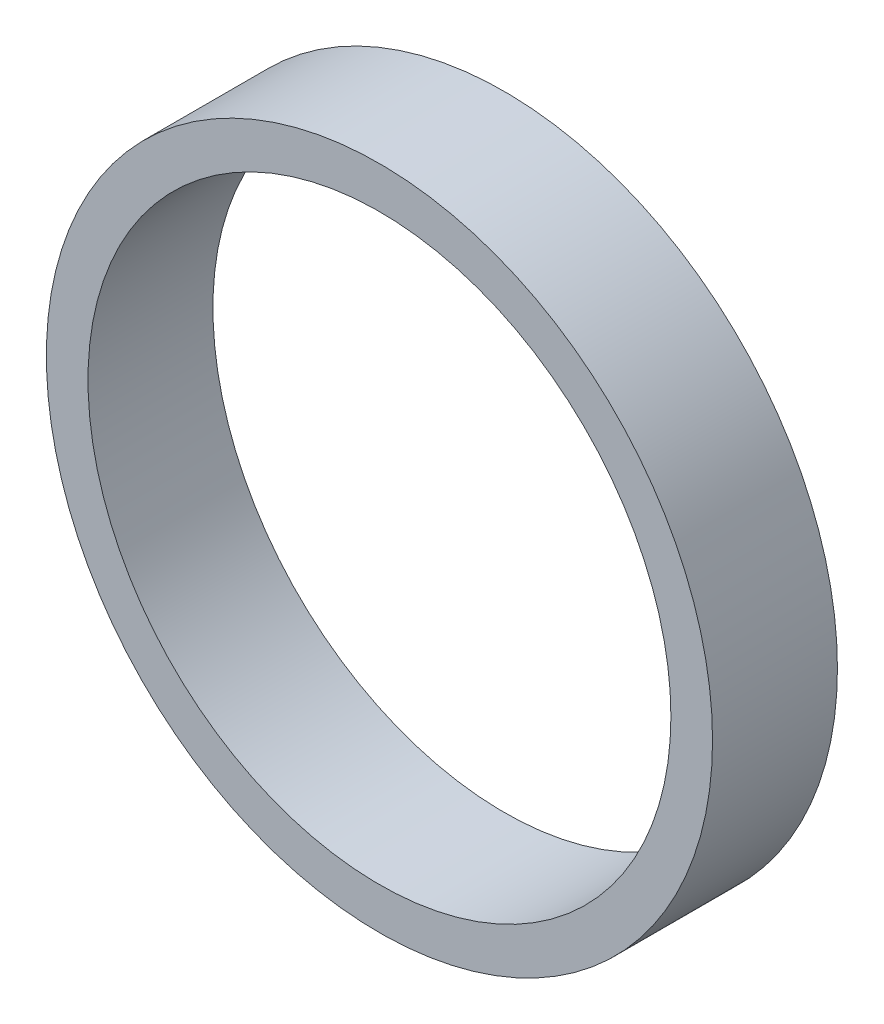
SolidWorks part; units mm, degrees
material "硅橡胶"
ref_plane "前视基准面" through (0, 0, 0) normal (0, 0, 1) x (1, 0, 0)
ref_plane "上视基准面" through (0, 0, 0) normal (0, 1, 0) x (1, 0, 0)
ref_plane "右视基准面" through (0, 0, 0) normal (1, 0, 0) x (0, 0, -1)
sketch "草图1" plane through (0, 0, 0) normal (0, 0, 1) x (1, 0, 0)
  circle A0 centre (0, 0) radius 14
  circle A1 centre (0, 0) radius 16
  dimension "D1" = 28
  dimension "D2" = 32
extrude "凸台-拉伸1" add sketch "草图1" along normal blind 6
